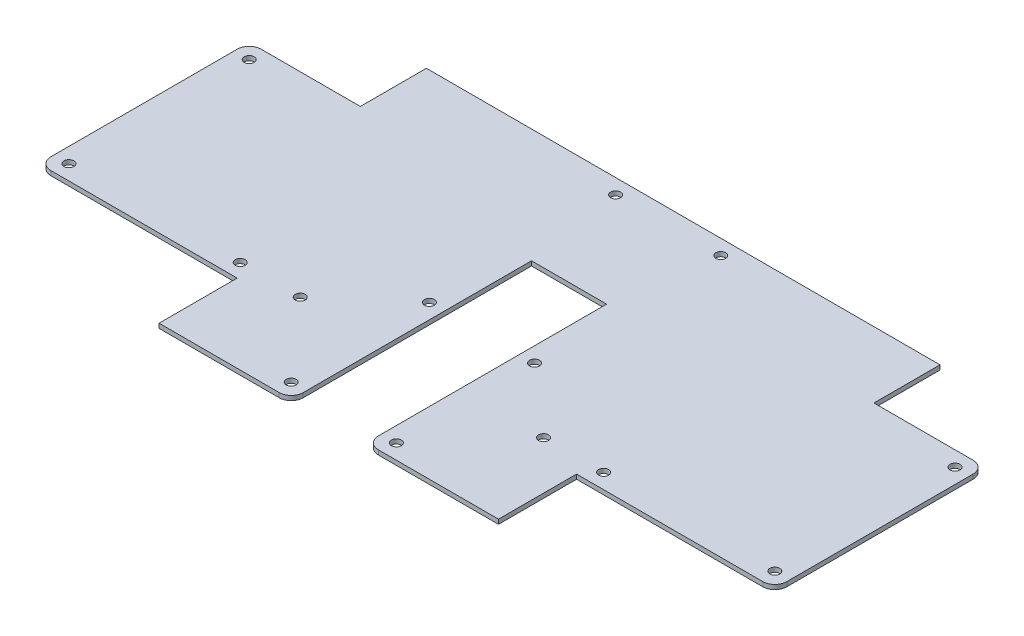
SolidWorks part; units mm, degrees
material "ABS PC"
ref_plane "Front Plane" through (0, 0, 0) normal (0, 0, 1) x (1, 0, 0)
ref_plane "Top Plane" through (0, 0, 0) normal (0, 1, 0) x (1, 0, 0)
ref_plane "Right Plane" through (0, 0, 0) normal (1, 0, 0) x (0, 0, -1)
sketch "Sketch1" plane through (0, 0, 0) normal (0, 1, 0) x (1, 0, 0)
  line L1 (0, 0) -> (245, 0)
  line L2 (0, 0) -> (0, 118)
  line L3 (0, 118) -> (245, 118)
  line L4 (245, 0) -> (245, 118)
  dimension "D1" = 245
  dimension "D2" = 118
extrude "Boss-Extrude1" add sketch "Sketch1" along normal blind 1.5
sketch "Sketch2" plane through (0, 1.5, 0) normal (0, 1, 0) x (1, 0, 0)
  line L1 (0, 118) -> (37, 118)
  line L2 (0, 118) -> (0, 96)
  line L3 (0, 96) -> (37, 96)
  line L4 (37, 118) -> (37, 96)
  line L5 (0, 0) -> (66, 0)
  line L6 (0, 0) -> (0, 26)
  line L7 (0, 26) -> (66, 26)
  line L8 (66, 0) -> (66, 26)
  line L9 (245, 118) -> (208, 118)
  line L10 (245, 118) -> (245, 96)
  line L11 (245, 96) -> (208, 96)
  line L12 (208, 118) -> (208, 96)
  line L13 (245, 0) -> (179, 0)
  line L14 (245, 0) -> (245, 26)
  line L15 (245, 26) -> (179, 26)
  line L16 (179, 0) -> (179, 26)
  line L17 (110, 0) -> (135, 0)
  line L18 (110, 0) -> (110, 80)
  line L19 (110, 80) -> (135, 80)
  line L20 (135, 0) -> (135, 80)
  dimension "D1" = 37
  dimension "D2" = 22
  dimension "D3" = 26
  dimension "D4" = 37
  dimension "D5" = 66
  dimension "D6" = 66
  dimension "D7" = 26
  dimension "D8" = 22
  dimension "D9" = 110
  dimension "D10" = 110
  dimension "D11" = 80
extrude "Cut-Extrude1" cut sketch "Sketch2" against normal through all
sketch "Sketch3" plane through (0, 0, 0) normal (0, -1, 0) x (1, 0, 0)
  line L0 (66, -26) -> (0, -26) construction
  line L1 (0, -96) -> (0, -26) construction
  line L2 (0, -96) -> (37, -96) construction
  line L3 (66, 0) -> (110, 0) construction
  line L4 (110, -80) -> (110, 0) construction
  line L5 (208, -118) -> (37, -118) construction
  line L6 (122.5, -80) -> (122.5, -118) construction
  line L7 (135, -80) -> (110, -80) construction
  line L9 (66, 0) -> (66, -26) construction
  circle A0 centre (5, -31) radius 1.65
  circle A1 centre (5, -91) radius 1.65
  circle A2 centre (105, -5) radius 1.65
  circle A3 centre (105, -51) radius 1.65
  circle A4 centre (105, -113) radius 1.65
  circle A5 centre (140, -51) radius 1.65
  circle A6 centre (140, -5) radius 1.65
  circle A7 centre (140, -113) radius 1.65
  circle A8 centre (240, -31) radius 1.65
  circle A9 centre (240, -91) radius 1.65
  circle A10 centre (62, -31) radius 1.65
  circle A11 centre (82, -31) radius 1.65
  circle A12 centre (163, -31) radius 1.65
  circle A13 centre (183, -31) radius 1.65
  dimension "D1" = 3.3
  dimension "D6" = 3.3
  dimension "D7" = 3.3
  dimension "D11" = 3.3
  dimension "D13" = 3.3
  dimension "D15" = 3.3
  dimension "D16" = 3.3
  dimension "D2" = 5
  dimension "D3" = 5
  dimension "D4" = 5
  dimension "D5" = 5
  dimension "D8" = 5
  dimension "D9" = 5
  dimension "D10" = 20
  dimension "D12" = 5
  dimension "D14" = 4
  dimension "D17" = 16
  dimension "D18" = 5
  dimension "D19" = 5
extrude "Cut-Extrude2" cut sketch "Sketch3" against normal blind 10
fillet "Fillet1" radius 4 6 edges at (110, 0.75, 0) (135, 0.75, 0) (245, 0.75, -26) (245, 0.75, -96) (0, 0.75, -26) (0, 0.75, -96)
